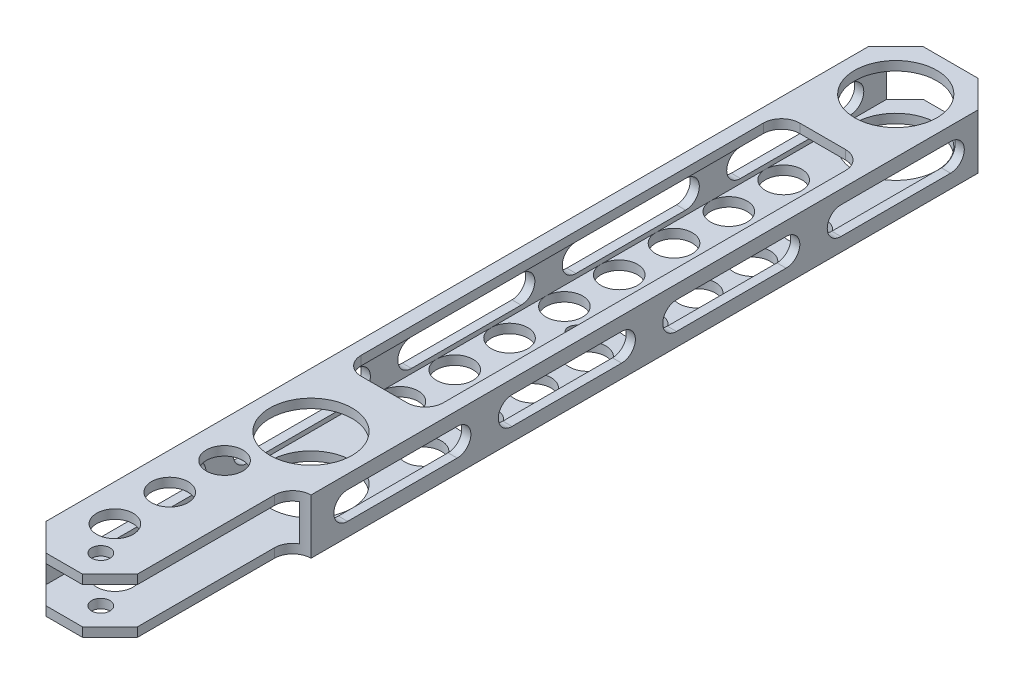
SolidWorks part; units mm, degrees
material "6063-T6"
ref_plane "Front" through (0, 0, 0) normal (0, 0, 1) x (1, 0, 0)
ref_plane "Top" through (0, 0, 0) normal (0, 1, 0) x (1, 0, 0)
ref_plane "Right" through (0, 0, 0) normal (1, 0, 0) x (0, 0, -1)
sketch "Sketch1" plane through (0, 0, 0) normal (0, 0, 1) x (1, 0, 0)
  line L0 (3.175, 3.175) -> (34.925, 3.175)
  line L1 (0, 0) -> (38.1, 0)
  line L2 (0, 0) -> (0, 19.05)
  line L3 (0, 19.05) -> (38.1, 19.05)
  line L4 (38.1, 0) -> (38.1, 19.05)
  line L5 (34.925, 3.175) -> (34.925, 15.875)
  line L6 (3.175, 15.875) -> (34.925, 15.875)
  line L7 (3.175, 3.175) -> (3.175, 15.875)
  dimension "D1" = 19.05
  dimension "D2" = 38.1
  dimension "D3" = 3.175
extrude "Boss-Extrude1" add sketch "Sketch1" along normal blind 304.8
sketch "Sketch13" plane through (0, 19.05, 0) normal (0, 1, 0) x (1, 0, 0)
  line L0 (38.1, -304.8) -> (45.8002, -312.8952) construction
sketch "Sketch2" plane through (0, 19.05, 0) normal (0, 1, 0) x (1, 0, 0)
  line L0 (19.05, 0) -> (19.05, -19.05) construction
  line L2 (19.05, -19.05) -> (19.05, -222.25) construction
  line L4 (38.1, -304.8) -> (38.1, 0) construction
  line L5 (38.1, 0) -> (0, 0) construction
  circle A0 centre (19.05, -19.05) radius 14.2875
  circle A1 centre (19.05, -222.25) radius 14.2875
  dimension "D1" = 28.575
  dimension "D4" = 28.575
  dimension "D2" = 19.05
  dimension "D3" = 203.2
  dimension "D5" = 19.05
extrude "Cut-Extrude1" cut sketch "Sketch2" against normal through all
sketch "Sketch3" plane through (0, 19.05, 0) normal (0, 1, 0) x (1, 0, 0)
  line L0 (19.05, -295.275) -> (19.05, -304.8) construction
  line L1 (38.1, -304.8) -> (0, -304.8) construction
  circle A0 centre (19.05, -295.275) radius 3.175
  dimension "D1" = 6.35
  dimension "D2" = 9.525
extrude "Cut-Extrude2" cut sketch "Sketch3" against normal through all
sketch "Sketch4" plane through (0, 19.05, 0) normal (0, 1, 0) x (1, 0, 0)
  line L0 (31.75, -304.8) -> (31.75, -247.65)
  line L1 (38.1, -304.8) -> (0, -304.8) construction
  line L2 (38.1, -241.3) -> (38.1, -304.8)
  line L3 (38.1, -304.8) -> (38.1, 0) construction
  line L4 (38.1, -304.8) -> (31.75, -304.8)
  arc A0 (38.1, -241.3) -> (31.75, -247.65) centre (38.1, -247.65) ccw
  dimension "D1" = 6.35
  dimension "D2" = 57.15
extrude "Cut-Extrude3" cut sketch "Sketch4" against normal through all
sketch "Sketch7" plane through (0, 0, 0) normal (-1, 0, 0) x (0, 0, 1)
  line L0 (19.05, 9.525) -> (57.15, 9.525) construction
  line L1 (19.05, 14.2875) -> (57.15, 14.2875)
  line L2 (19.05, 4.7625) -> (57.15, 4.7625)
  line L3 (34.9537, 14.2875) -> (34.9537, 19.05) construction
  line L4 (304.8, 19.05) -> (0, 19.05) construction
  line L5 (40.4377, 4.7625) -> (40.4377, 0) construction
  line L6 (304.8, 0) -> (0, 0) construction
  line L7 (0, 19.05) -> (0, 0) construction
  line L8 (92.1037, 14.2875) -> (92.1037, 19.05) construction
  line L9 (97.5877, 4.7625) -> (97.5877, 0) construction
  line L10 (76.2, 9.525) -> (114.3, 9.525) construction
  line L11 (76.2, 14.2875) -> (114.3, 14.2875)
  line L12 (76.2, 4.7625) -> (114.3, 4.7625)
  line L13 (149.2537, 14.2875) -> (149.2537, 19.05) construction
  line L14 (154.7377, 4.7625) -> (154.7377, 0) construction
  line L15 (133.35, 9.525) -> (171.45, 9.525) construction
  line L18 (133.35, 14.2875) -> (171.45, 14.2875)
  line L19 (133.35, 4.7625) -> (171.45, 4.7625)
  line L20 (206.4037, 14.2875) -> (206.4037, 19.05) construction
  line L21 (211.8877, 4.7625) -> (211.8877, 0) construction
  line L24 (190.5, 9.525) -> (228.6, 9.525) construction
  line L25 (190.5, 14.2875) -> (228.6, 14.2875)
  line L26 (190.5, 4.7625) -> (228.6, 4.7625)
  line L27 (263.5537, 14.2875) -> (263.5537, 19.05) construction
  line L28 (269.0377, 4.7625) -> (269.0377, 0) construction
  line L29 (247.65, 9.525) -> (285.75, 9.525) construction
  line L30 (247.65, 14.2875) -> (285.75, 14.2875)
  line L31 (247.65, 4.7625) -> (285.75, 4.7625)
  arc A0 (19.05, 14.2875) -> (19.05, 4.7625) centre (19.05, 9.525) ccw
  arc A1 (57.15, 4.7625) -> (57.15, 14.2875) centre (57.15, 9.525) ccw
  arc A2 (76.2, 14.2875) -> (76.2, 4.7625) centre (76.2, 9.525) ccw
  arc A3 (114.3, 4.7625) -> (114.3, 14.2875) centre (114.3, 9.525) ccw
  arc A6 (133.35, 14.2875) -> (133.35, 4.7625) centre (133.35, 9.525) ccw
  arc A7 (171.45, 4.7625) -> (171.45, 14.2875) centre (171.45, 9.525) ccw
  arc A10 (190.5, 14.2875) -> (190.5, 4.7625) centre (190.5, 9.525) ccw
  arc A11 (228.6, 4.7625) -> (228.6, 14.2875) centre (228.6, 9.525) ccw
  arc A12 (247.65, 14.2875) -> (247.65, 4.7625) centre (247.65, 9.525) ccw
  arc A13 (285.75, 4.7625) -> (285.75, 14.2875) centre (285.75, 9.525) ccw
  point P2 (38.1, 9.525)
  point P20 (95.25, 9.525)
  point P30 (152.4, 9.525)
  point P41 (209.55, 9.525)
  point P52 (266.7, 9.525)
  dimension "D1" = 9.525
  dimension "D2" = 38.1
  dimension "D3" = 19.05
  dimension "D5" = 19.05
  dimension "D4" = 5
extrude "Cut-Extrude6" cut sketch "Sketch7" against normal through all
sketch "Sketch8" plane through (0, 19.05, 0) normal (0, 1, 0) x (1, 0, 0)
  line L0 (0, -79.7679) -> (4.7625, -79.7679) construction
  line L1 (11.1125, -44.45) -> (26.9875, -44.45)
  line L2 (4.7625, -50.8) -> (4.7625, -190.5)
  line L3 (11.1125, -196.85) -> (26.9875, -196.85)
  line L4 (33.3375, -50.8) -> (33.3375, -190.5)
  line L5 (4.7625, -44.45) -> (33.3375, -196.85) construction
  line L6 (4.7625, -196.85) -> (33.3375, -44.45) construction
  line L7 (0, -304.8) -> (0, 0) construction
  line L8 (33.3375, -93.6616) -> (38.1, -93.6616) construction
  line L9 (38.1, -241.3) -> (38.1, 0) construction
  line L10 (19.05, -19.05) -> (19.05, -44.45) construction
  line L11 (19.05, -222.25) -> (19.05, -196.85) construction
  arc A1 (26.9875, -196.85) -> (33.3375, -190.5) centre (26.9875, -190.5) ccw
  arc A2 (4.7625, -190.5) -> (11.1125, -196.85) centre (11.1125, -190.5) ccw
  arc A3 (11.1125, -44.45) -> (4.7625, -50.8) centre (11.1125, -50.8) ccw
  arc A4 (26.9875, -44.45) -> (33.3375, -50.8) centre (26.9875, -50.8) cw
  point P4 (19.05, -120.65)
  dimension "D3" = 6.35
  dimension "D1" = 4.7625
  dimension "D2" = 152.4
extrude "Cut-Extrude7" cut sketch "Sketch8" against normal up to next
sketch "Sketch9" plane through (0, 0, 0) normal (0, -1, 0) x (1, 0, 0)
  line L0 (9.525, 48.4757) -> (0, 48.4757) construction
  line L1 (0, 304.8) -> (0, 0) construction
  line L2 (28.575, 59.4743) -> (38.1, 59.4743) construction
  line L3 (38.1, 241.3) -> (38.1, 0) construction
  line L4 (9.525, 48.4757) -> (28.575, 59.4743) construction
  line L6 (28.575, 59.4743) -> (18.7516, 59.4743) construction
  line L7 (19.05, 19.05) -> (9.525, 48.4757) construction
  line L8 (28.575, 192.8243) -> (19.05, 222.25) construction
  circle A0 centre (9.525, 48.4757) radius 6.35
  circle A1 centre (28.575, 59.4743) radius 6.35
  circle A2 centre (9.525, 67.5257) radius 6.35
  circle A3 centre (28.575, 78.5243) radius 6.35
  circle A4 centre (9.525, 86.5757) radius 6.35
  circle A5 centre (28.575, 97.5743) radius 6.35
  circle A6 centre (9.525, 105.6257) radius 6.35
  circle A7 centre (28.575, 116.6243) radius 6.35
  circle A8 centre (9.525, 124.6757) radius 6.35
  circle A9 centre (28.575, 135.6743) radius 6.35
  circle A10 centre (9.525, 143.7257) radius 6.35
  circle A11 centre (28.575, 154.7243) radius 6.35
  circle A12 centre (9.525, 162.7757) radius 6.35
  circle A13 centre (28.575, 173.7743) radius 6.35
  circle A14 centre (9.525, 181.8257) radius 6.35
  circle A15 centre (28.575, 192.8243) radius 6.35
  dimension "D1" = 12.7
  dimension "D3" = 12.7
  dimension "D2" = 9.525
  dimension "D4" = 8
  dimension "D5" = 30
extrude "Cut-Extrude8" cut sketch "Sketch9" against normal up to next
sketch "Sketch10" plane through (0, 0, 0) normal (0, -1, 0) x (1, 0, 0)
  line L0 (19.05, 130.175) -> (38.1, 130.175) construction
  line L1 (38.1, 241.3) -> (38.1, 0) construction
  line L2 (19.05, 130.175) -> (0, 130.175) construction
  line L3 (0, 304.8) -> (0, 0) construction
  line L4 (19.05, 19.05) -> (19.05, 130.175) construction
  circle A0 centre (19.05, 130.175) radius 2.667
  dimension "D1" = 5.334
extrude "Cut-Extrude9" cut sketch "Sketch10" against normal up to next
sketch "Sketch11" plane through (0, 19.05, 0) normal (0, 1, 0) x (1, 0, 0)
  line L0 (12.7, -245.9272) -> (0, -245.9272) construction
  line L5 (0, -304.8) -> (0, 0) construction
  circle A0 centre (12.7, -245.9272) radius 6.35
  circle A1 centre (12.7, -264.9772) radius 6.35
  circle A2 centre (12.7, -284.0272) radius 6.35
  dimension "D1" = 12.7
  dimension "D2" = 12.7
  dimension "D3" = 3
extrude "Cut-Extrude10" cut sketch "Sketch11" against normal through all
sketch "Sketch12" plane through (0, 19.05, 0) normal (0, 1, 0) x (1, 0, 0)
  line L0 (28.575, 0) -> (38.1, -9.525)
  line L1 (38.1, 0) -> (0, 0) construction
  line L2 (38.1, -241.3) -> (38.1, 0) construction
  line L3 (38.1, -9.525) -> (38.1, 0)
  line L4 (38.1, 0) -> (28.575, 0)
  line L5 (19.05, 0) -> (19.05, -13.0808) construction
  line L6 (0, 0) -> (9.525, 0)
  line L7 (0, -9.525) -> (0, 0)
  line L8 (9.525, 0) -> (0, -9.525)
  line L9 (0, -152.4) -> (60.0019, -152.4) construction
  line L10 (0, -304.8) -> (0, 0) construction
  line L11 (9.525, -304.8) -> (0, -295.275)
  line L12 (0, -295.275) -> (0, -304.8)
  line L13 (0, -304.8) -> (9.525, -304.8)
  line L14 (15.875, -304.8) -> (15.875, -299.8407) construction
  line L15 (31.75, -304.8) -> (0, -304.8) construction
  line L16 (31.75, -304.8) -> (22.225, -304.8)
  line L17 (31.75, -295.275) -> (31.75, -304.8)
  line L18 (22.225, -304.8) -> (31.75, -295.275)
  dimension "D1" = 9.525
extrude "Cut-Extrude11" cut sketch "Sketch12" against normal through all
sketch "Sketch14" plane through (0, 19.05, 0) normal (0, 1, 0) x (1, 0, 0)
  point P0 (26.9875, -50.8)
  point P1 (11.1125, -50.8)
  point P3 (26.9875, -190.5)
  point P5 (11.1125, -190.5)
